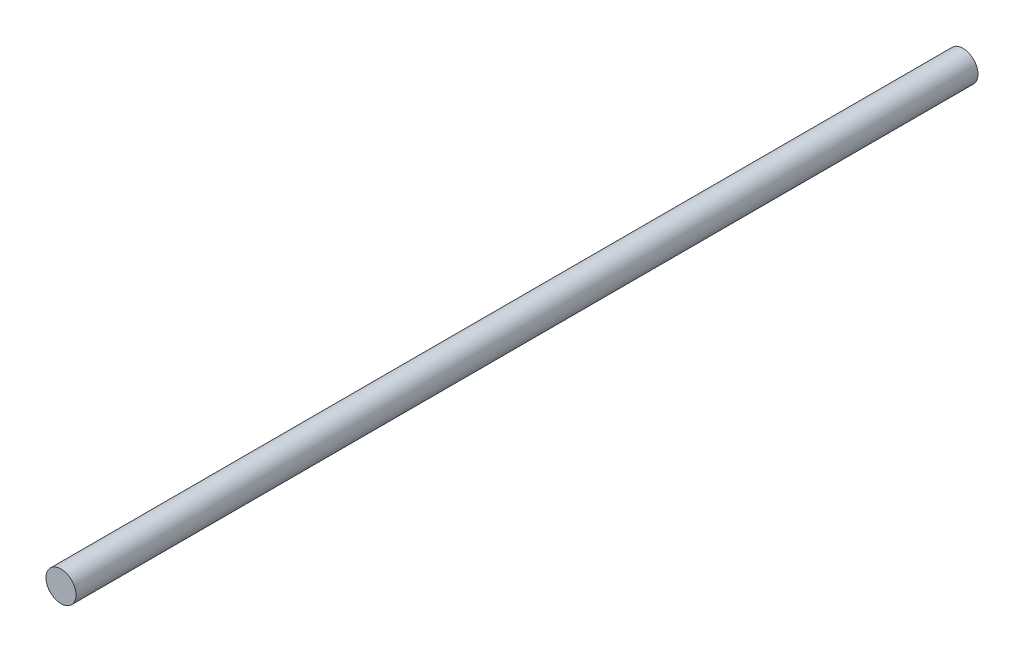
SolidWorks part; units mm, degrees
ref_plane "Alzado" through (0, 0, 0) normal (0, 0, 1) x (1, 0, 0)
ref_plane "Planta" through (0, 0, 0) normal (0, 1, 0) x (1, 0, 0)
ref_plane "Vista lateral" through (0, 0, 0) normal (1, 0, 0) x (0, 0, -1)
sketch "Croquis1" plane through (0, 0, 0) normal (0, 0, 1) x (1, 0, 0)
  circle A0 centre (0, 0) radius 5
  dimension "D1" = 10
extrude "Saliente-Extruir1" add sketch "Croquis1" along normal blind 300
